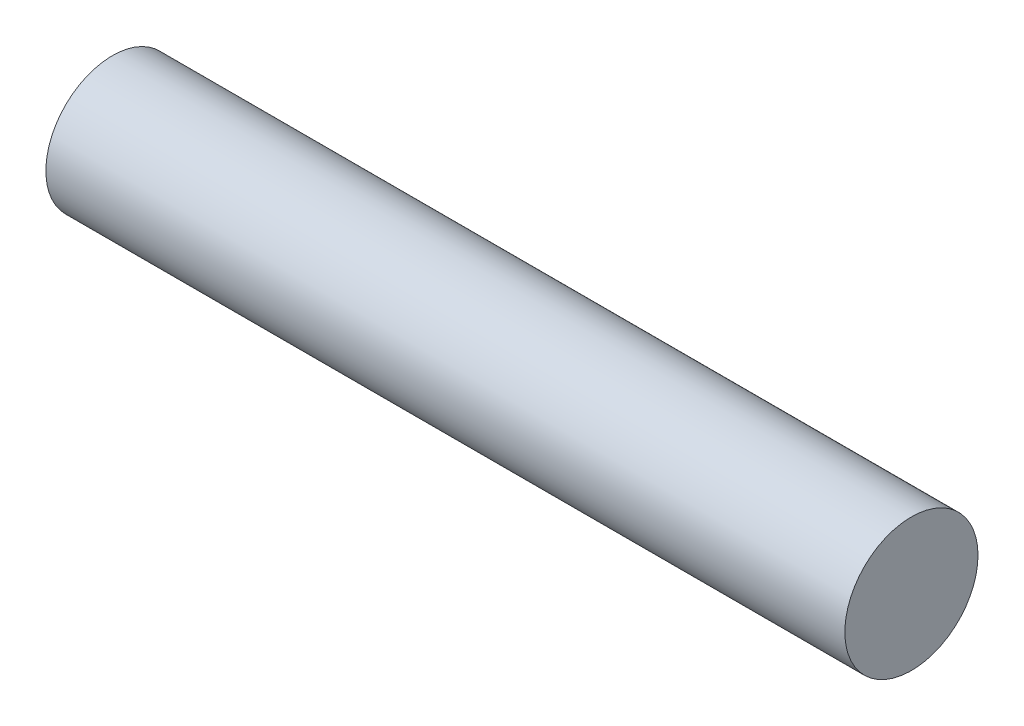
SolidWorks part; units mm, degrees
ref_plane "Alzado" through (0, 0, 0) normal (0, 0, 1) x (1, 0, 0)
ref_plane "Planta" through (0, 0, 0) normal (0, 1, 0) x (1, 0, 0)
ref_plane "Vista lateral" through (0, 0, 0) normal (1, 0, 0) x (0, 0, -1)
sketch "Croquis1" plane through (0, 0, 0) normal (1, 0, 0) x (0, 0, -1)
  circle A0 centre (0, 0) radius 3.175
  dimension "D1" = 6.35
extrude "Saliente-Extruir1" add sketch "Croquis1" along normal blind 38.1
